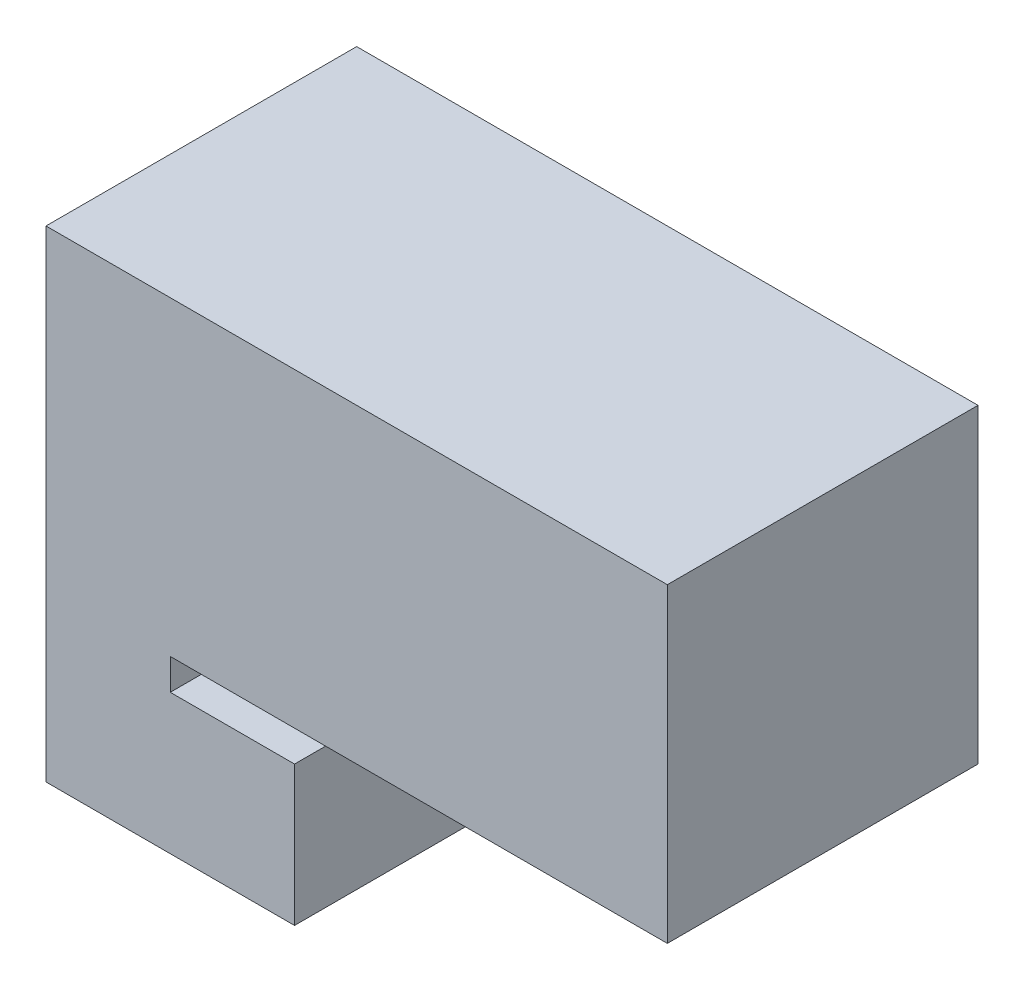
SolidWorks part; units mm, degrees
ref_plane "Front Plane" through (0, 0, 0) normal (0, 0, 1) x (1, 0, 0)
ref_plane "Top Plane" through (0, 0, 0) normal (0, 1, 0) x (1, 0, 0)
ref_plane "Right Plane" through (0, 0, 0) normal (1, 0, 0) x (0, 0, -1)
sketch "Sketch1" plane through (0, 0, 0) normal (0, 0, 1) x (1, 0, 0)
  line L0 (0, 0) -> (0, 28.575)
  line L1 (0, 28.575) -> (-25.4, 28.575)
  line L2 (-25.4, 28.575) -> (-25.4, 98.425)
  line L3 (-25.4, 98.425) -> (-50.8, 98.425)
  line L4 (-50.8, 98.425) -> (-50.8, 0)
  line L5 (-50.8, 0) -> (0, 0)
  dimension "D1" = 50.8
  dimension "D2" = 98.425
  dimension "D3" = 25.4
  dimension "D4" = 25.4
  dimension "D5" = 28.575
extrude "Boss-Extrude1" add sketch "Sketch1" along normal blind 63.5 contours L4 L5 L0 L1 L2 L3
sketch "Sketch2" plane through (-25.4, 0, 0) normal (1, 0, 0) x (0, 0, -1)
  line L0 (-63.5, 28.575) -> (-63.5, 98.425) construction
  line L1 (-63.5, 34.925) -> (0, 34.925)
  line L2 (-63.5, 34.925) -> (-63.5, 98.425)
  line L3 (-63.5, 98.425) -> (0, 98.425)
  line L4 (0, 34.925) -> (0, 98.425)
  dimension "D1" = 63.5
extrude "Boss-Extrude2" add sketch "Sketch2" along normal blind 101.6
